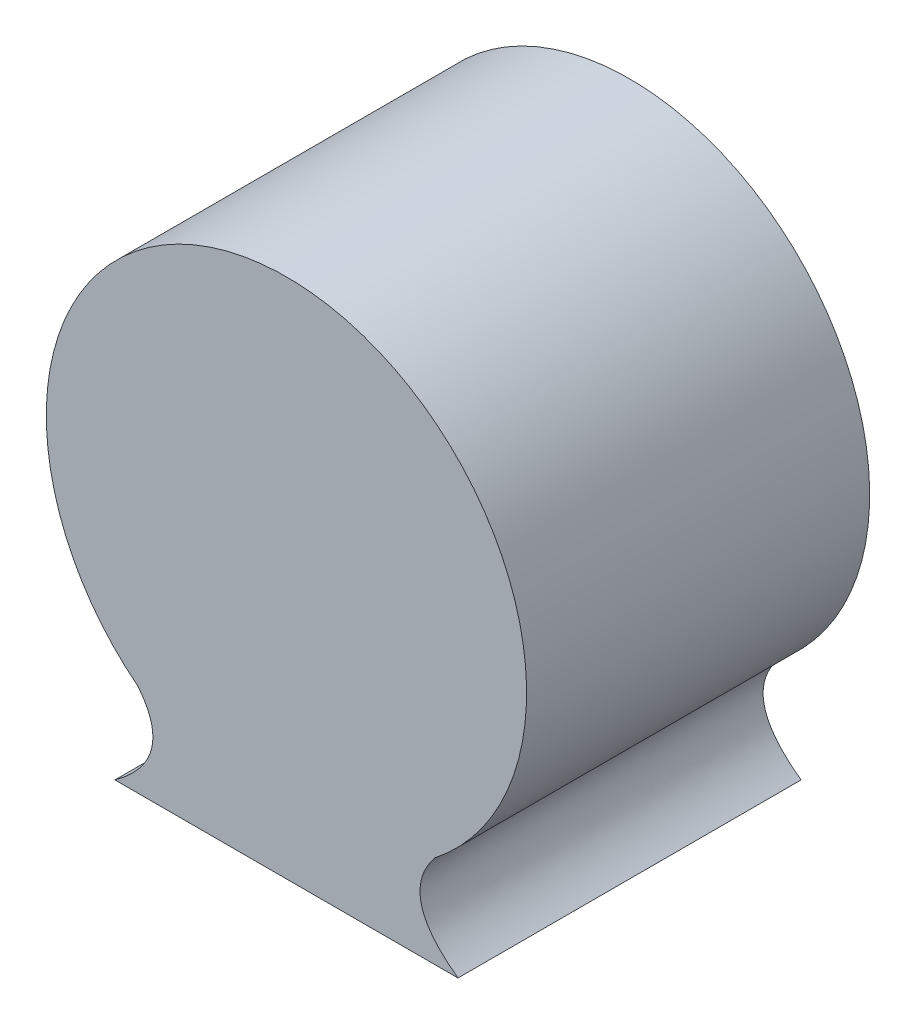
SolidWorks part; units mm, degrees
ref_plane "Płaszczyzna przednia" through (0, 0, 0) normal (0, 0, 1) x (1, 0, 0)
ref_plane "Płaszczyzna górna" through (0, 0, 0) normal (0, 1, 0) x (1, 0, 0)
ref_plane "Płaszczyzna prawa" through (0, 0, 0) normal (1, 0, 0) x (0, 0, -1)
sketch "Szkic1" plane through (0, 0, 0) normal (0, 0, 1) x (1, 0, 0)
  line L0 (0, 0) -> (0, -41) construction
  line L1 (25, -41) -> (-25, -41)
  arc A0 (21.6267, -27.5188) -> (-21.6267, -27.5188) centre (0, 0) ccw
  spline S0 degree 2 poles (-25, -41) (-16.0098, -34.5135) (-21.6267, -27.5188) knots 0 0 0 1 1 1
  spline S1 degree 2 poles (25, -41) (16.0098, -34.5135) (21.6267, -27.5188) knots 0 0 0 1 1 1
  point P7 (0, -41)
  dimension "D1" = 41
  dimension "D2" = 70
  dimension "D3" = 50
extrude "Dodanie-wyciągnięcie1" add sketch "Szkic1" along normal blind 50
sketch "Szkic2" plane through (0, 0, 50) normal (0, 0, 1) x (1, 0, 0)
  circle A0 centre (0, 0) radius 28.2774
sketch "Szkic3" plane through (0, -41, 0) normal (0, -1, 0) x (1, 0, 0)
  line L0 (0, 50) -> (0, 0) construction
  line L1 (-25, 50) -> (25, 50) construction
  line L2 (-25, 0) -> (25, 0) construction
  line L3 (-25, 25) -> (25, 25) construction
  line L4 (-25, 50) -> (-25, 0) construction
  line L5 (25, 50) -> (25, 0) construction
  circle A0 centre (0, 25) radius 20.0059
